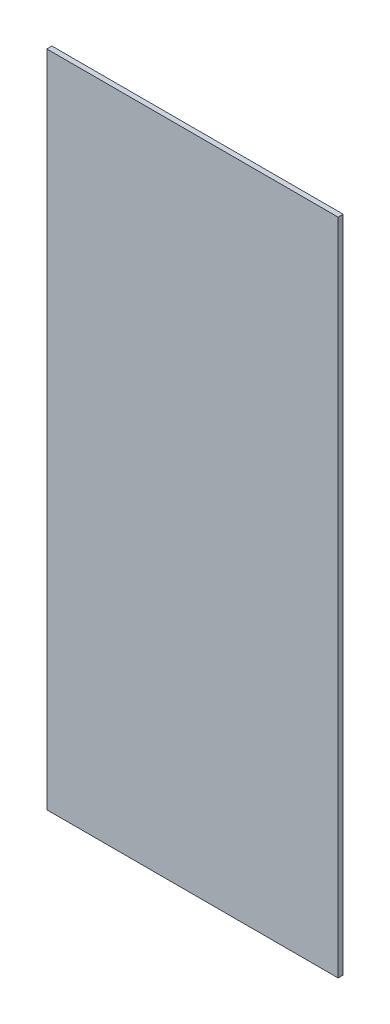
SolidWorks part; units mm, degrees
ref_plane "Front Plane" through (0, 0, 0) normal (0, 0, 1) x (1, 0, 0)
ref_plane "Top Plane" through (0, 0, 0) normal (0, 1, 0) x (1, 0, 0)
ref_plane "Right Plane" through (0, 0, 0) normal (1, 0, 0) x (0, 0, -1)
sketch "Sketch1" plane through (0, 0, 0) normal (0, 0, 1) x (1, 0, 0)
  line L1 (-287.5, 650.25) -> (287.5, 650.25)
  line L2 (-287.5, 650.25) -> (-287.5, -650.25)
  line L3 (-287.5, -650.25) -> (287.5, -650.25)
  line L4 (287.5, 650.25) -> (287.5, -650.25)
  line L5 (-287.5, 650.25) -> (287.5, -650.25) construction
  line L6 (-287.5, -650.25) -> (287.5, 650.25) construction
  point P0 (0, 0)
  dimension "D1" = 575
  dimension "D2" = 1300.5
extrude "Boss-Extrude1" add sketch "Sketch1" along normal blind 10
